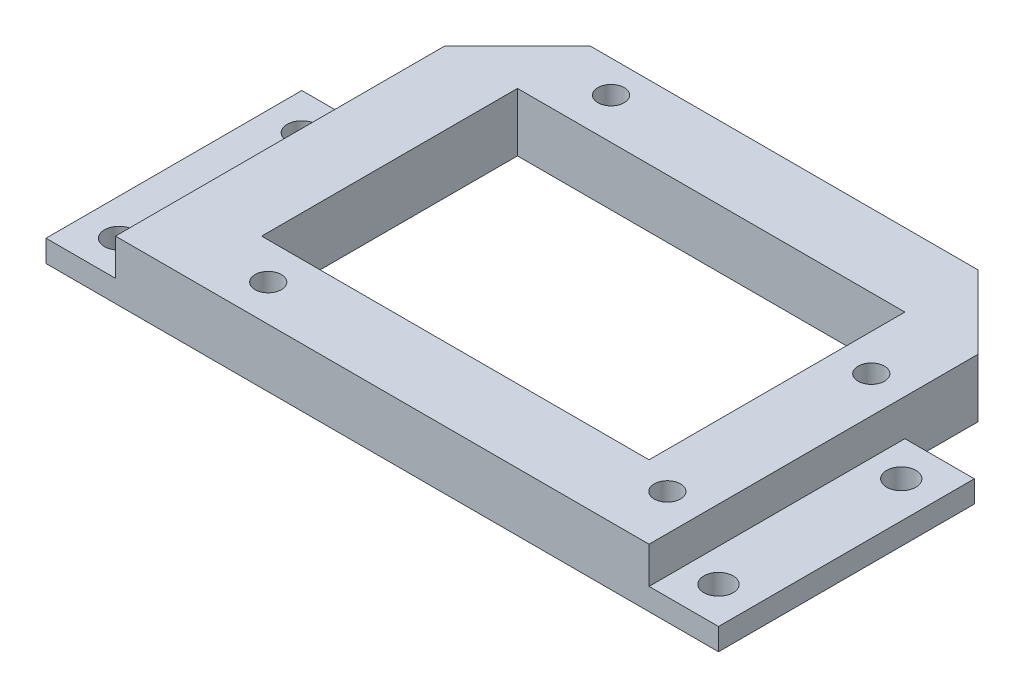
SolidWorks part; units mm, degrees
ref_plane "Front Plane" through (0, 0, 0) normal (0, 0, 1) x (1, 0, 0)
ref_plane "Top Plane" through (0, 0, 0) normal (0, 1, 0) x (1, 0, 0)
ref_plane "Right Plane" through (0, 0, 0) normal (1, 0, 0) x (0, 0, -1)
sketch "Sketch1" plane through (0, 0, 0) normal (0, 1, 0) x (1, 0, 0)
  line L1 (-36.5, -17.5) -> (36.5, -17.5)
  line L2 (-36.5, -17.5) -> (-36.5, 17.5)
  line L3 (-36.5, 17.5) -> (36.5, 17.5)
  line L4 (36.5, -17.5) -> (36.5, 17.5)
  line L5 (-36.5, -17.5) -> (36.5, 17.5) construction
  line L6 (-36.5, 17.5) -> (36.5, -17.5) construction
  point P0 (0, 0)
  dimension "D1" = 73
  dimension "D2" = 35
extrude "Boss-Extrude1" add sketch "Sketch1" along normal blind 5
sketch "Sketch2" plane through (0, 0, 0) normal (0, -1, 0) x (1, 0, 0)
  line L0 (-36.5, 17.5) -> (36.5, 17.5) construction
  line L1 (-46, -17.5) -> (46, -17.5)
  line L2 (-46, -17.5) -> (-46, 17.5)
  line L3 (-46, 17.5) -> (46, 17.5)
  line L4 (46, -17.5) -> (46, 17.5)
  line L5 (-46, -17.5) -> (46, 17.5) construction
  line L6 (-46, 17.5) -> (46, -17.5) construction
  point P0 (0, 0)
  dimension "D1" = 92
extrude "Boss-Extrude2" add sketch "Sketch2" along normal blind 3
sketch "Sketch3" plane through (0, 0, 0) normal (0, 1, 0) x (1, 0, 0)
  line L1 (-40.5, -15.25) -> (40.5, -15.25)
  line L2 (-40.5, -15.25) -> (-40.5, 15.25)
  line L3 (-40.5, 15.25) -> (40.5, 15.25)
  line L4 (40.5, -15.25) -> (40.5, 15.25)
  line L5 (-40.5, -15.25) -> (40.5, 15.25) construction
  line L6 (-40.5, 15.25) -> (40.5, -15.25) construction
  point P0 (0, 0)
  dimension "D1" = 30.5
  dimension "D2" = 81
hole_wizard "M3 Clearance Hole1" positions "Sketch7" profile "Sketch8" hole size "M3" standard "ANSI Metric"
sketch "Sketch7" plane through (0, 0, 0) normal (0, 1, 0) x (1, 0, 0)
  line L0 (-46, 17.5) -> (-36.5, 17.5) construction
  line L1 (36.5, 17.5) -> (46, 17.5) construction
  line L2 (46, -17.5) -> (36.5, -17.5) construction
  line L3 (-36.5, -17.5) -> (-46, -17.5) construction
  line L4 (-46, -17.5) -> (-46, 17.5) construction
  line L5 (46, 17.5) -> (46, -17.5) construction
  point P0 (-41, 12.5)
  point P2 (-41, -12.5)
  point P4 (41, 12.5)
  point P6 (41, -12.5)
  dimension "D1" = 5
  dimension "D2" = 5
  dimension "D3" = 5
  dimension "D4" = 5
  dimension "D5" = 5
  dimension "D6" = 5
sketch "Sketch8" plane through (-41, 0, -12.5) normal (1, 0, 0) x (0, 0, 1)
  line L0 (0, 0) -> (0, 11.2017)
  line L1 (0, 11.2017) -> (2, 10)
  line L2 (2, 10) -> (2, 0)
  line L5 (2, 0) -> (0, 0)
  line L10 (0, 11.2017) -> (-2, 10) construction
  line L11 (0, -6.35) -> (0, 107.95) construction
  dimension "Hole Dia." = 4
  dimension "Hole Depth" = 10
  dimension "Drill Angle" = 118
sketch "Sketch9" plane through (0, 0, -17.5) normal (0, 0, -1) x (-1, 0, 0)
  line L0 (-36.5, 5) -> (36.5, 5) construction
  line L1 (-36.5, 5) -> (36.5, 5)
  line L2 (-36.5, 5) -> (-36.5, -3)
  line L3 (-36.5, -3) -> (36.5, -3)
  line L4 (36.5, 5) -> (36.5, -3)
  line L5 (46, -3) -> (-46, -3) construction
  line L6 (-36.5, 5) -> (-36.5, 0) construction
  line L7 (36.5, 5) -> (36.5, 0) construction
extrude "Boss-Extrude3" add sketch "Sketch9" along normal blind 20
hole_wizard "M3 Clearance Hole3" positions "Sketch10" profile "Sketch11" hole size "M3" standard "ANSI Metric"
sketch "Sketch10" plane through (0, 5, 0) normal (0, 1, 0) x (1, 0, 0)
  line L11 (-36.5, -17.5) -> (36.5, -17.5) construction
  line L13 (36.5, -17.5) -> (36.5, 37.5) construction
  point P140 (-20.6, -12.5)
  point P142 (-19.3, 33.1)
  point P144 (31.5, -10)
  point P146 (31.5, 17.9)
  point P149 (0, 0)
  point P150 (0, 0)
  point P151 (-16.2373, 24.0856)
  point P152 (-23.4737, -27.2322)
  point P153 (-23.8364, 33.2184)
  point P154 (-25.527, 31.9808)
  dimension "D1" = 1.3
  dimension "D2" = 27.9
  dimension "D3" = 15.2
  dimension "D4" = 50.8
  dimension "D5" = 2.5
  dimension "D6" = 5
  dimension "D7" = 5
sketch "Sketch11" plane through (-20.6, 5, 12.5) normal (1, 0, 0) x (0, 0, 1)
  line L0 (0, 0) -> (0, 11.0815)
  line L1 (0, 11.0815) -> (1.8, 10)
  line L2 (1.8, 10) -> (1.8, 0)
  line L5 (1.8, 0) -> (0, 0)
  line L10 (0, 11.0815) -> (-1.8, 10) construction
  line L11 (0, -6.35) -> (0, 107.95) construction
  dimension "Hole Dia." = 3.6
  dimension "Hole Depth" = 10
  dimension "Drill Angle" = 118
sketch "Sketch12" plane through (0, 5, 0) normal (0, 1, 0) x (1, 0, 0)
  line L8 (26.5, -7.5) -> (26.5, 27.5)
  line L9 (26.5, 27.5) -> (-26.5, 27.5)
  line L10 (-26.5, 27.5) -> (-26.5, -7.5)
  line L11 (-26.5, -7.5) -> (26.5, -7.5)
  line L12 (26.5, -7.5) -> (26.5, 27.5)
  line L13 (26.5, 27.5) -> (-26.5, 27.5)
  line L14 (-26.5, 27.5) -> (-26.5, -7.5)
  line L15 (-26.5, -7.5) -> (26.5, -7.5)
  dimension "D1" = 10
extrude "Cut-Extrude1" cut sketch "Sketch12" against normal through all
chamfer "Chamfer1" distance 10 angle 45 2 edges at (-36.5, 1, -37.5) (36.5, 1, -37.5)
equation "\"8`\"=84.8464"
